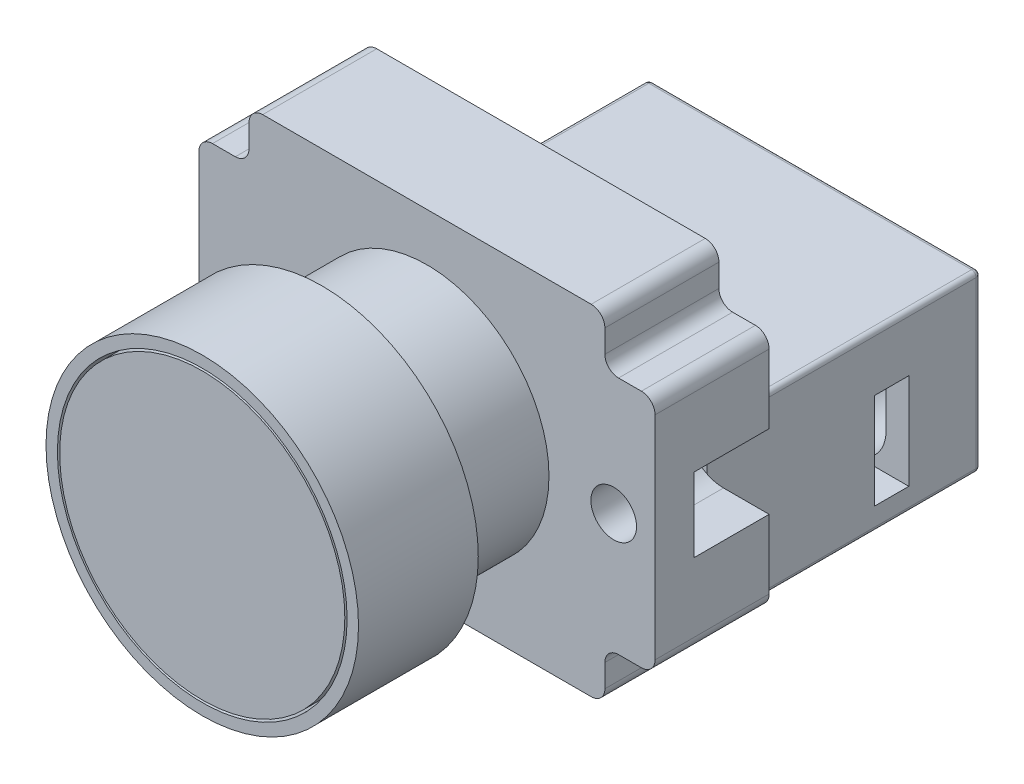
SolidWorks part; units mm, degrees
ref_plane "Front Plane" through (0, 0, 0) normal (0, 0, 1) x (1, 0, 0)
ref_plane "Top Plane" through (0, 0, 0) normal (0, 1, 0) x (1, 0, 0)
ref_plane "Right Plane" through (0, 0, 0) normal (1, 0, 0) x (0, 0, -1)
sketch "Sketch1" plane through (0, 0, 0) normal (0, 0, 1) x (1, 0, 0)
  circle A0 centre (0, 0) radius 10.7
  dimension "D1" = 21.4
extrude "Boss-Extrude1" add sketch "Sketch1" along normal mid plane 9.2
sketch "Sketch2" plane through (0, 0, 0) normal (0, 0, 1) x (1, 0, 0)
  circle A0 centre (0, 0) radius 13.7
  circle A1 centre (0, 0) radius 12.7
  dimension "D1" = 27.4
  dimension "D2" = 1
extrude "Boss-Extrude2" add sketch "Sketch2" along normal blind 10.5 from surface at 4.6 separate body starting at face at (10.7, 0, 4.6)
sketch "Sketch3" plane through (0, 0, 0) normal (0, 0, 1) x (1, 0, 0)
  circle A0 centre (0, 0) radius 12.5
  circle A1 centre (0, 0) radius 12.7 construction
  dimension "D1" = 0.2
extrude "Boss-Extrude3" add sketch "Sketch3" along normal up to surface (10.5 mm away) from surface at 4.6 up to face at (13.7, 0, 15.1) starting at face at (10.7, 0, 4.6)
sketch "Sketch4" plane through (0, 0, 0) normal (0, 0, 1) x (1, 0, 0)
  line L1 (-20, -14.9) -> (20, -14.9)
  line L2 (-20, -14.9) -> (-20, 14.9)
  line L3 (-20, 14.9) -> (20, 14.9)
  line L4 (20, -14.9) -> (20, 14.9)
  line L5 (-20, -14.9) -> (20, 14.9) construction
  line L6 (-20, 14.9) -> (20, -14.9) construction
  line L7 (20, 14.9) -> (15.6, 14.9)
  line L8 (20, 14.9) -> (20, 10.5)
  line L9 (20, 10.5) -> (15.6, 10.5)
  line L10 (15.6, 14.9) -> (15.6, 10.5)
  line L11 (20, -14.9) -> (15.6, -14.9)
  line L12 (20, -14.9) -> (20, -10.5)
  line L13 (20, -10.5) -> (15.6, -10.5)
  line L14 (15.6, -14.9) -> (15.6, -10.5)
  line L15 (-20, -14.9) -> (-15.6, -14.9)
  line L16 (-20, -14.9) -> (-20, -10.5)
  line L17 (-20, -10.5) -> (-15.6, -10.5)
  line L18 (-15.6, -14.9) -> (-15.6, -10.5)
  line L19 (-20, 14.9) -> (-15.6, 14.9)
  line L20 (-20, 14.9) -> (-20, 10.5)
  line L21 (-20, 10.5) -> (-15.6, 10.5)
  line L22 (-15.6, 14.9) -> (-15.6, 10.5)
  point P0 (0, 0)
  dimension "D1" = 40
  dimension "D2" = 29.8
  dimension "D3" = 4.4
extrude "Boss-Extrude4" add sketch "Sketch4" against normal blind 10 from surface at -4.6 contours L3 L22 L21 L2 L17 L18 L1 L14 L13 L4 L9 L10 starting at face at (10.7, 0, -4.6)
fillet "Fillet1" radius 1.2 12 edges at (15.6, -10.5, -9.6) (-15.6, -10.5, -9.6) (-15.6, 10.5, -9.6) (15.6, 10.5, -9.6) (-15.6, -14.9, -9.6) (-20, -10.5, -9.6) (15.6, -14.9, -9.6) (20, -10.5, -9.6) (20, 10.5, -9.6) (15.6, 14.9, -9.6) (-20, 10.5, -9.6) (-15.6, 14.9, -9.6)
sketch "Sketch5" plane through (0, 0, 0) normal (0, 0, 1) x (1, 0, 0)
  line L0 (20, -9.3) -> (20, 9.3) construction
  line L1 (20, 3.25) -> (16, 3.25)
  line L2 (20, 3.25) -> (20, -3.25)
  line L3 (20, -3.25) -> (16, -3.25)
  line L4 (16, 3.25) -> (16, -3.25)
  line L5 (-20, -9.3) -> (-20, 9.3) construction
  line L6 (-20, 3.25) -> (-16, 3.25)
  line L7 (-20, 3.25) -> (-20, -3.25)
  line L8 (-20, -3.25) -> (-16, -3.25)
  line L9 (-16, 3.25) -> (-16, -3.25)
  arc A0 (16, 3.25) -> (16, -3.25) centre (16, 0) ccw
  arc A1 (-16, 3.25) -> (-16, -3.25) centre (-16, 0) cw
  point P12 (20, 0)
  point P13 (20, 0)
  dimension "D1" = 6.5
  dimension "D2" = 4
extrude "Cut-Extrude1" cut sketch "Sketch5" along normal offset from surface (6.6 mm away) 3.4 from surface at -14.6 contours L1 L4 L3 L2 | L4 A0 | A1 L9 | L9 L6 L7 L8 up to face at (10.7, 0, -4.6) starting at face at (0, 0, -14.6)
sketch "Sketch6" plane through (0, 0, 0) normal (0, 0, 1) x (1, 0, 0)
  line L0 (20, 3.25) -> (20, -3.25) construction
  line L1 (16.375, 0) -> (12.75, 0) construction
  line L2 (-16.375, 0) -> (-12.75, 0) construction
  line L3 (-16.375, 0) -> (-20, 0) construction
  line L4 (-20, 3.25) -> (-20, -3.25) construction
  line L5 (16.375, 0) -> (20, 0) construction
  circle A0 centre (16.375, 0) radius 2
  circle A1 centre (-16.375, 0) radius 2
  arc A2 (16, 3.25) -> (16, -3.25) centre (16, 0) ccw construction
  arc A3 (-16, -3.25) -> (-16, 3.25) centre (-16, 0) ccw construction
  point P7 (20, 0)
  dimension "D1" = 4
extrude "Cut-Extrude2" cut sketch "Sketch6" along normal up to next (4.6 mm away) from surface at -8 starting at face at (17.1875, 0, -8)
sketch "Sketch7" plane through (0, 0, 0) normal (0, 0, 1) x (1, 0, 0)
  line L0 (-14.4, -14.9) -> (14.4, -14.9) construction
  line L1 (14.55, -14.7) -> (-14.55, -14.7)
  line L2 (14.55, -14.7) -> (14.55, 0.6)
  line L3 (14.55, 0.6) -> (-14.55, 0.6)
  line L4 (-14.55, -14.7) -> (-14.55, 0.6)
  point P6 (0, -14.9)
  point P7 (0, -14.7)
  dimension "D1" = 15.3
  dimension "D2" = 29.1
  dimension "D3" = 0.2
extrude "Boss-Extrude5" add sketch "Sketch7" against normal blind 24 from surface at -14.6 starting at face at (0, 0, -14.6)
fillet "Fillet2" radius 0.4 8 edges at (-14.55, -7.05, -38.6) (0, -14.7, -38.6) (0, 0.6, -38.6) (14.55, -7.05, -38.6) (-14.55, -14.7, -26.6) (-14.55, 0.6, -26.6) (14.55, -14.7, -26.6) (14.55, 0.6, -26.6)
sketch "Sketch8" plane through (0, 0, 0) normal (0, 0, 1) x (1, 0, 0)
  circle A0 centre (0, 0) radius 10.9
  dimension "D1" = 21.8
extrude "Cut-Extrude3" cut sketch "Sketch8" along normal blind 4.8 from surface at -14.6 starting at face at (0, 8.725, -14.6)
sketch "Sketch9" plane through (0, 0, 0) normal (0, 0, 1) x (1, 0, 0)
  line L0 (-14.15, -14.3) -> (-14.15, 0.2) construction
  line L1 (12.55, -5.6) -> (6.15, -5.6)
  line L2 (12.55, -5.6) -> (12.55, -9.5)
  line L3 (12.55, -9.5) -> (6.15, -9.5)
  line L4 (6.15, -5.6) -> (6.15, -9.5)
  line L5 (-6.15, -5.6) -> (-12.55, -5.6)
  line L6 (-6.15, -5.6) -> (-6.15, -9.5)
  line L7 (-6.15, -9.5) -> (-12.55, -9.5)
  line L8 (-12.55, -5.6) -> (-12.55, -9.5)
  line L9 (14.15, 0.2) -> (14.15, -14.3) construction
  line L10 (-14.15, 0.2) -> (14.15, 0.2) construction
  arc A0 (12.55, -9.5) -> (6.15, -9.5) centre (9.35, -9.5) cw
  arc A1 (-6.15, -9.5) -> (-12.55, -9.5) centre (-9.35, -9.5) cw
  dimension "D1" = 3.9
  dimension "D2" = 6.4
  dimension "D3" = 1.6
  dimension "D4" = 1.6
  dimension "D5" = 5.8
extrude "Cut-Extrude4" cut sketch "Sketch9" along normal blind 9 from surface at -38.6 contours L1 L4 L3 L2 | A0 L3 | L5 L8 L7 L6 | A1 L7 starting at face at (0, -7.05, -38.6)
sketch "Sketch10" plane through (0, 0, 0) normal (1, 0, 0) x (0, 0, -1)
  line L0 (38.2, -14.3) -> (14.6, -14.3) construction
  line L1 (32.3, -4.3) -> (29.3, -4.3)
  line L2 (32.3, -4.3) -> (32.3, -12.7)
  line L3 (32.3, -12.7) -> (29.3, -12.7)
  line L4 (29.3, -4.3) -> (29.3, -12.7)
  line L5 (38.2, 0.2) -> (38.2, -14.3) construction
  dimension "D1" = 3
  dimension "D2" = 8.4
  dimension "D3" = 1.6
  dimension "D4" = 5.9
extrude "Cut-Extrude5" cut sketch "Sketch10" along normal blind 11 from surface at -14.55 starting at face at (-14.55, -6.2217, -24.04)
sketch "Sketch11" plane through (0, 0, 0) normal (1, 0, 0) x (0, 0, -1)
  line L0 (29.3, -4.3) -> (32.3, -4.3) construction
  line L1 (29.3, -4.3) -> (32.3, -4.3)
  line L2 (29.3, -4.3) -> (29.3, -12.7)
  line L3 (29.3, -12.7) -> (32.3, -12.7)
  line L4 (32.3, -4.3) -> (32.3, -12.7)
  line L5 (32.3, -12.7) -> (29.3, -12.7) construction
  line L6 (32.3, -4.3) -> (32.3, -12.7) construction
  line L7 (29.3, -12.7) -> (29.3, -4.3) construction
extrude "Cut-Extrude6" cut sketch "Sketch11" against normal blind 11 from surface at 14.55 starting at face at (14.55, -6.2217, -24.04)
